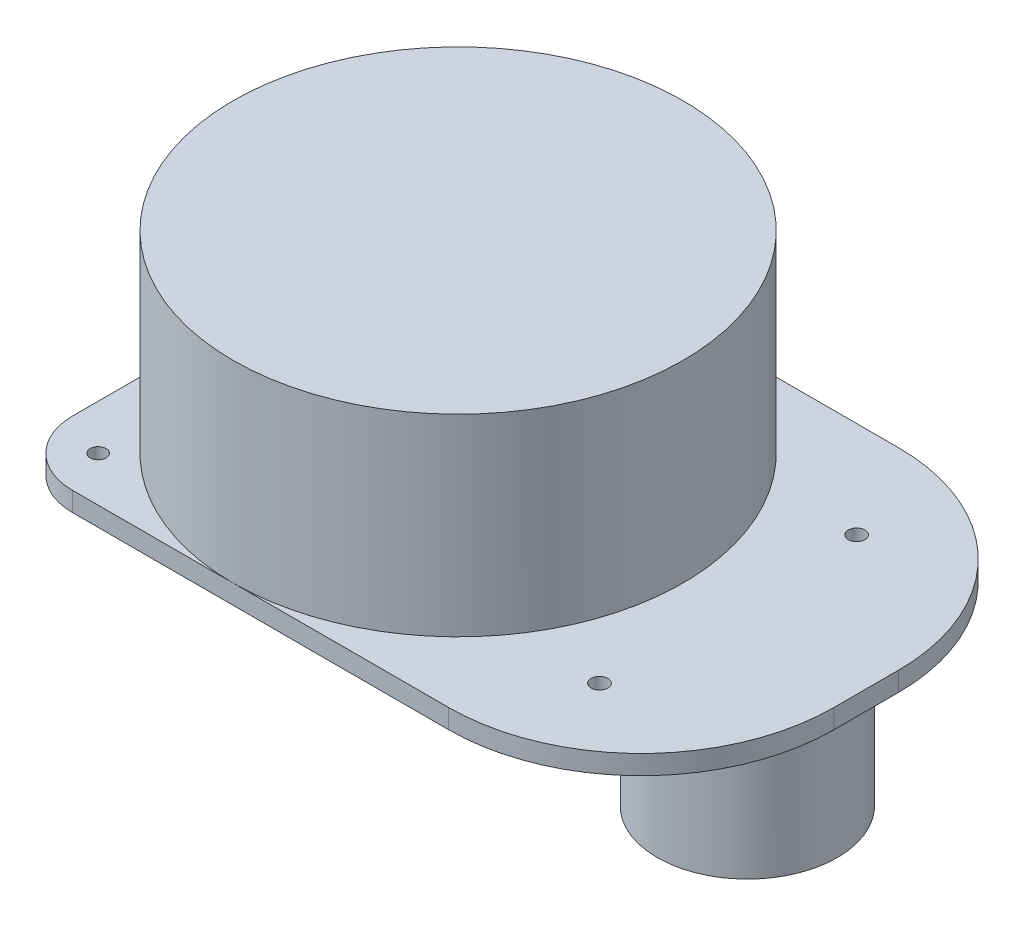
SolidWorks part; units mm, degrees
ref_plane "Front Plane" through (0, 0, 0) normal (0, 0, 1) x (1, 0, 0)
ref_plane "Top Plane" through (0, 0, 0) normal (0, 1, 0) x (1, 0, 0)
ref_plane "Right Plane" through (0, 0, 0) normal (1, 0, 0) x (0, 0, -1)
sketch "스케치1" plane through (0, 0, 0) normal (0, 1, 0) x (1, 0, 0)
  circle A0 centre (0, 0) radius 35
extrude "보스-돌출1" add sketch "스케치1" along normal blind 30
sketch "스케치2" plane through (0, 0, 0) normal (0, -1, 0) x (1, 0, 0)
  line L1 (-35, -35) -> (63.5, -35)
  line L2 (-35, -35) -> (-35, 35)
  line L3 (-35, 35) -> (63.5, 35)
  line L4 (63.5, -35) -> (63.5, 35)
  dimension "D1" = 35
  dimension "D2" = 70
  dimension "D3" = 35
  dimension "D4" = 63.5
extrude "보스-돌출2" add sketch "스케치2" along normal blind 3
fillet "필렛1" radius 10 2 edges at (-35, -1.5, 35) (-35, -1.5, -35)
fillet "필렛2" radius 30 1 edges at (63.5, -1.5, -35)
fillet "필렛3" radius 30 1 edges at (63.5, -1.5, 35)
sketch "스케치3" plane through (0, 0, 0) normal (0, 1, 0) x (1, 0, 0)
  line L0 (0, 0) -> (0, 50000) construction
  line L1 (-28, -2.8053) -> (-28, 49997.1947) construction
  line L2 (42, -3.1006) -> (42, 49996.8994) construction
  line L3 (0, 28) -> (50000, 28) construction
  line L4 (0, 0) -> (50000, 0) construction
  line L5 (0, -28) -> (50000, -28) construction
  line L6 (-54.6532, 20) -> (49945.3468, 20) construction
  line L7 (-51.7002, -20) -> (49948.2998, -20) construction
  circle A0 centre (-28, 28) radius 1.3
  circle A1 centre (-28, -28.0042) radius 1.2528
  circle A2 centre (42, 20) radius 1.3
  circle A3 centre (42, -20) radius 1.3
  dimension "D5" = 28
  dimension "D1" = 20
  dimension "D2" = 20
  dimension "D3" = 28
  dimension "D4" = 28
  dimension "D6" = 42
extrude "컷-돌출1" cut sketch "스케치3" against normal blind 3
sketch "스케치4" plane through (0, -3, 0) normal (0, -1, 0) x (1, 0, 0)
  line L0 (0, 0) -> (50000, 0) construction
  line L1 (45, 0) -> (45, -50000) construction
  line L2 (0, 0) -> (0, -50000) construction
  circle A0 centre (45, 0) radius 14
  dimension "D1" = 45
extrude "보스-돌출3" add sketch "스케치4" along normal blind 22
